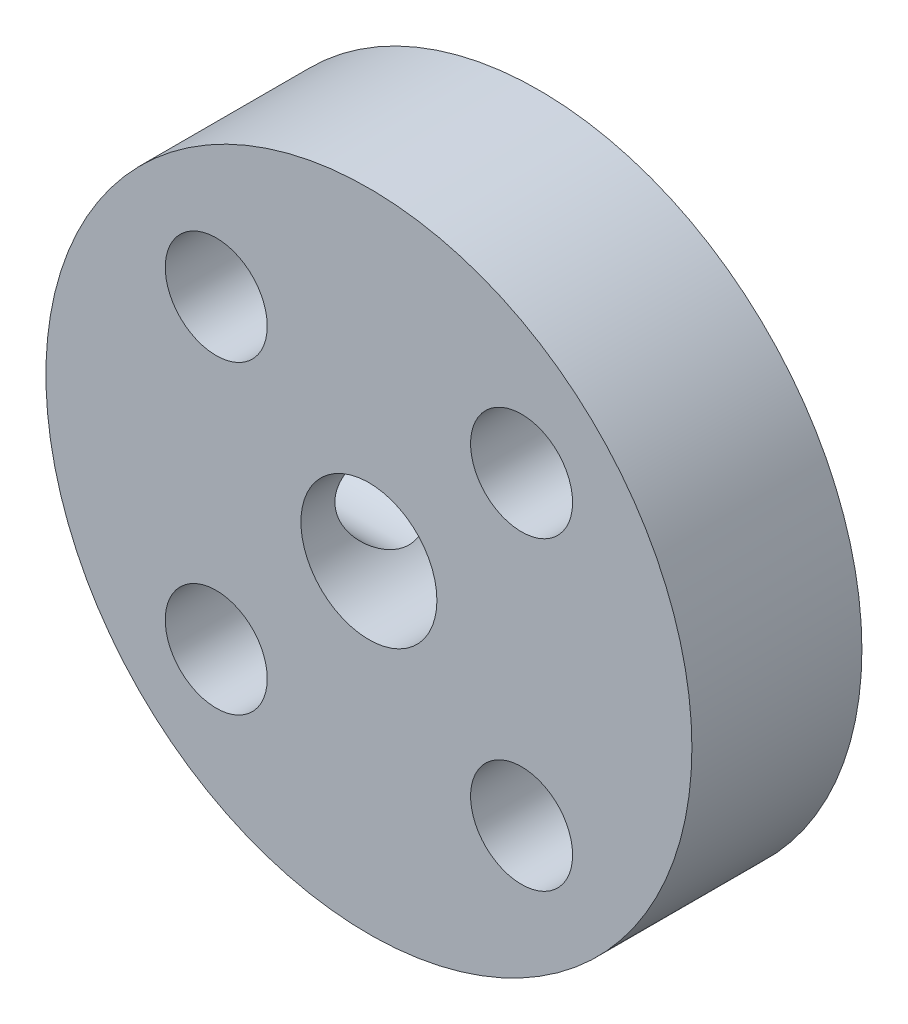
SolidWorks part; units mm, degrees
ref_plane "Plan de face" through (0, 0, 0) normal (0, 0, 1) x (1, 0, 0)
ref_plane "Plan de dessus" through (0, 0, 0) normal (0, 1, 0) x (1, 0, 0)
ref_plane "Plan de droite" through (0, 0, 0) normal (1, 0, 0) x (0, 0, -1)
sketch "Esquisse1" plane through (0, 0, 0) normal (0, 0, 1) x (1, 0, 0)
  line L0 (-10.314, 10.314) -> (11.202, -11.202) construction
  line L1 (-8.9482, -8.9482) -> (12.5223, 12.5223) construction
  line L2 (0, 0) -> (-13.7891, 0) construction
  circle A0 centre (0, 0) radius 9.5
  circle A1 centre (0, 0) radius 2
  circle A2 centre (4.4901, 4.4901) radius 1.5
  circle A3 centre (4.4901, -4.4901) radius 1.5
  circle A4 centre (-4.4901, 4.4901) radius 1.5
  circle A5 centre (-4.4901, -4.4901) radius 1.5
  circle A6 centre (0, 0) radius 6.35 construction
  point P15 (0, 0)
  point P16 (-5.8874, 2.3792)
  point P17 (3.1988, 5.4855)
  point P19 (-4.8901, 4.0509)
  point P20 (-2.8669, -5.666)
  point P22 (5.1041, -3.7776)
  point P23 (0, 0)
  point P24 (0, 0)
  point P25 (0, 0)
  point P26 (0, 0)
  dimension "D1" = 19
  dimension "D2" = 4
  dimension "D3" = 3
  dimension "D4" = 12.7
  dimension "D5" = 45
  dimension "D6" = 90
  dimension "D7" = 45
extrude "Boss.-Extru.1" add sketch "Esquisse1" along normal mid plane 5
sketch "Esquisse2" plane through (0, 0, 0) normal (1, 0, 0) x (0, 0, -1)
  circle A0 centre (0, 0) radius 1.5
  point P2 (0, 0)
  dimension "D1" = 3
extrude "Enlèv. mat.-Extru.1" cut sketch "Esquisse2" against normal blind 16
